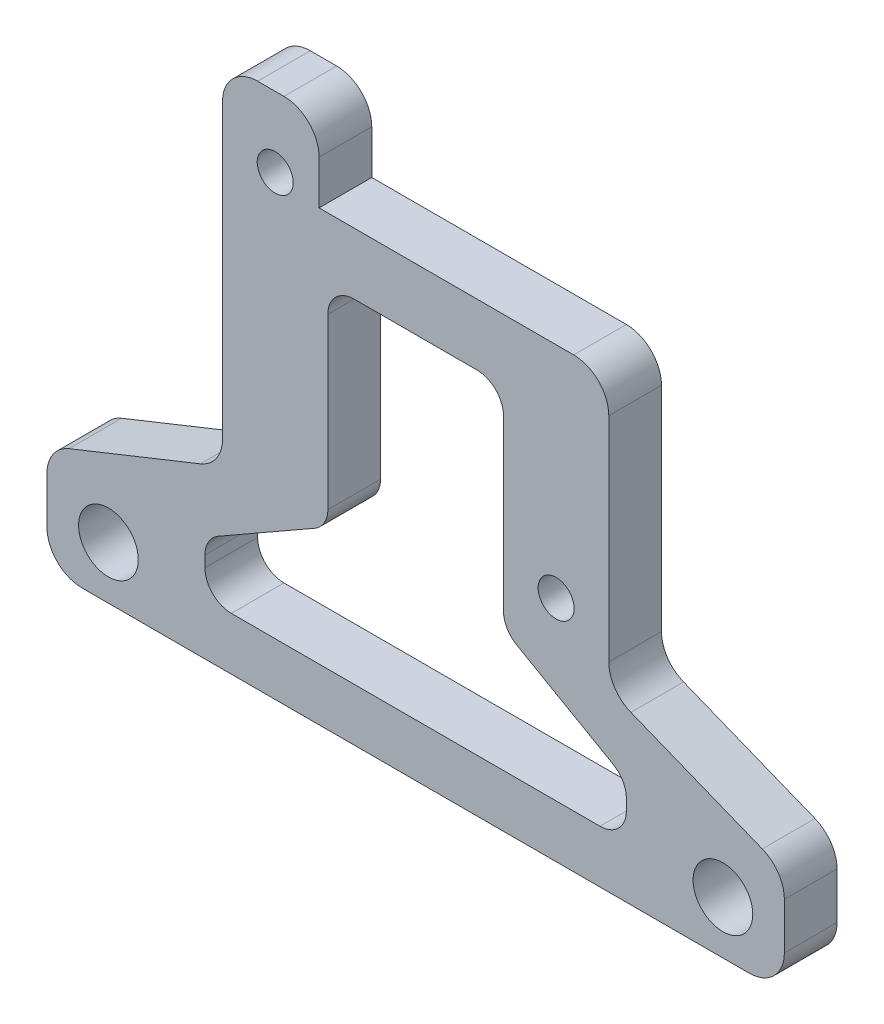
SolidWorks part; units mm, degrees
ref_plane "Front Plane" through (0, 0, 0) normal (0, 0, 1) x (1, 0, 0)
ref_plane "Top Plane" through (0, 0, 0) normal (0, 1, 0) x (1, 0, 0)
ref_plane "Right Plane" through (0, 0, 0) normal (1, 0, 0) x (0, 0, -1)
sketch "Sketch1" plane through (0, 0, 0) normal (0, 0, 1) x (1, 0, 0)
  line L0 (0, 52.4179) -> (0, -8.0946) construction
  line L1 (-21, 0) -> (21, 0)
  line L2 (-21, 0) -> (-21, 6)
  line L3 (-21, 6) -> (-11, 10)
  line L4 (21, 0) -> (21, 6)
  line L5 (-11, 30) -> (11, 30)
  line L10 (-11, 30) -> (-11, 10)
  line L11 (21, 6) -> (11, 10)
  line L12 (11, 30) -> (11, 10)
  circle A0 centre (-8, 26) radius 0.5
  circle A1 centre (8, 13) radius 0.5
  circle A2 centre (-17.5, 3) radius 0.5
  circle A3 centre (17.5, 3) radius 0.5
  point P12 (0, 0)
  point P27 (0, 30)
  dimension "D1" = 1
  dimension "D2" = 1
  dimension "D6" = 1
  dimension "D7" = 1
  dimension "D3" = 6
  dimension "D4" = 42
  dimension "D5" = 22
  dimension "D8" = 20
  dimension "D9" = 3
  dimension "D10" = 4
  dimension "D11" = 3
  dimension "D12" = 3
  dimension "D13" = 10
  dimension "D14" = 35
  dimension "D15" = 17.5
  dimension "D16" = 3
extrude "Boss-Extrude1" add sketch "Sketch1" along normal blind 3
hole_wizard "M2.5x0.45 Tapped Hole1" positions "Sketch2" profile "Sketch3" tap size "M2.5x0.45" standard "ANSI Metric" end condition through all
sketch "Sketch2" plane through (0, 0, 3) normal (0, 0, 1) x (1, 0, 0)
  point P0 (-8, 26)
  point P3 (8, 13)
sketch "Sketch3" plane through (-8, 26, 3) normal (1, 0, 0) x (0, -1, 0)
  line L0 (0, 0) -> (0, 3)
  line L1 (0, 3) -> (1.025, 3)
  line L2 (1.025, 3) -> (1.025, 0)
  line L5 (1.025, 0) -> (0, 0)
  line L11 (0, -6.35) -> (0, 107.95) construction
  dimension "Thru Tap Drill Dia." = 2.05
  dimension "Thru Tap Drill Depth" = 3
cosmetic thread "Hole Thread1" parameters "D2"=2.5
cosmetic thread "Hole Thread2" parameters "D2"=2.5
sketch "Sketch4" plane through (0, 0, 3) normal (0, 0, 1) x (1, 0, 0)
  line L0 (-5.5, 30) -> (-5.5, 25.5)
  line L1 (11, 30) -> (-11, 30) construction
  line L2 (-5.5, 25.5) -> (11, 25.5)
  line L3 (11, 10) -> (11, 30) construction
  line L4 (11, 25.5) -> (11, 30)
  line L5 (11, 30) -> (-5.5, 30)
  line L6 (0, 0) -> (0, 30) construction
  line L7 (-3.5, 22) -> (3.5, 22)
  line L8 (-5, 20.5) -> (-5, 10.8705)
  line L10 (5, 20.5) -> (5, 10.8705)
  line L12 (-21, 0) -> (21, 0) construction
  line L13 (5.7558, 9.5681) -> (11.2442, 6.4319)
  line L14 (12, 5.1295) -> (12, 4.5)
  line L15 (10.5, 3) -> (-10.5, 3)
  line L16 (-12, 4.5) -> (-12, 5.1295)
  line L17 (-11.2442, 6.4319) -> (-5.7558, 9.5681)
  line L18 (-21, 0) -> (21, 0) construction
  circle A0 centre (-8, 26) radius 1.025 construction
  arc A1 (-12, 5.1295) -> (-11.2442, 6.4319) centre (-10.5, 5.1295) cw
  arc A2 (11.2442, 6.4319) -> (12, 5.1295) centre (10.5, 5.1295) cw
  arc A3 (-3.5, 22) -> (-5, 20.5) centre (-3.5, 20.5) ccw
  arc A4 (3.5, 22) -> (5, 20.5) centre (3.5, 20.5) cw
  arc A5 (-5, 10.8705) -> (-5.7558, 9.5681) centre (-6.5, 10.8705) cw
  arc A6 (5.7558, 9.5681) -> (5, 10.8705) centre (6.5, 10.8705) cw
  arc A7 (-10.5, 3) -> (-12, 4.5) centre (-10.5, 4.5) cw
  arc A8 (12, 4.5) -> (10.5, 3) centre (10.5, 4.5) cw
  point P27 (0, 3)
  point P29 (-12, 6)
  point P32 (12, 6)
  point P39 (-5, 10)
  point P42 (5, 10)
  point P47 (12, 3)
  dimension "D1" = 2.5
  dimension "D5" = 24
  dimension "D9" = 1.5
  dimension "D10" = 1.5
  dimension "D2" = 4.5
  dimension "D3" = 10
  dimension "D4" = 22
  dimension "D6" = 3
  dimension "D7" = 3
  dimension "D8" = 7
extrude "Cut-Extrude1" cut sketch "Sketch4" against normal through all
fillet "Fillet1" radius 2 7 edges at (-5.5, 30, 1.5) (11, 25.5, 1.5) (11, 10, 1.5) (21, 6, 1.5) (-11, 10, 1.5) (-21, 6, 1.5) (-11, 30, 1.5)
hole_wizard "M3 Clearance Hole1" positions "Sketch5" profile "Sketch6" hole size "M3" standard "ANSI Metric" end condition up to next
sketch "Sketch5" plane through (0, 0, 3) normal (0, 0, 1) x (1, 0, 0)
  point P0 (-17.5, 3)
  point P3 (17.5, 3)
sketch "Sketch6" plane through (-17.5, 3, 3) normal (1, 0, 0) x (0, -1, 0)
  line L0 (0, 0) -> (0, 3)
  line L1 (0, 3) -> (1.7, 3)
  line L2 (1.7, 3) -> (1.7, 0)
  line L5 (1.7, 0) -> (0, 0)
  line L11 (0, -6.35) -> (0, 107.95) construction
  dimension "Thru Hole Dia." = 3.4
  dimension "Thru Hole Depth" = 3
fillet "Fillet2" radius 2 2 edges at (21, 0, 1.5) (-21, 0, 1.5)
